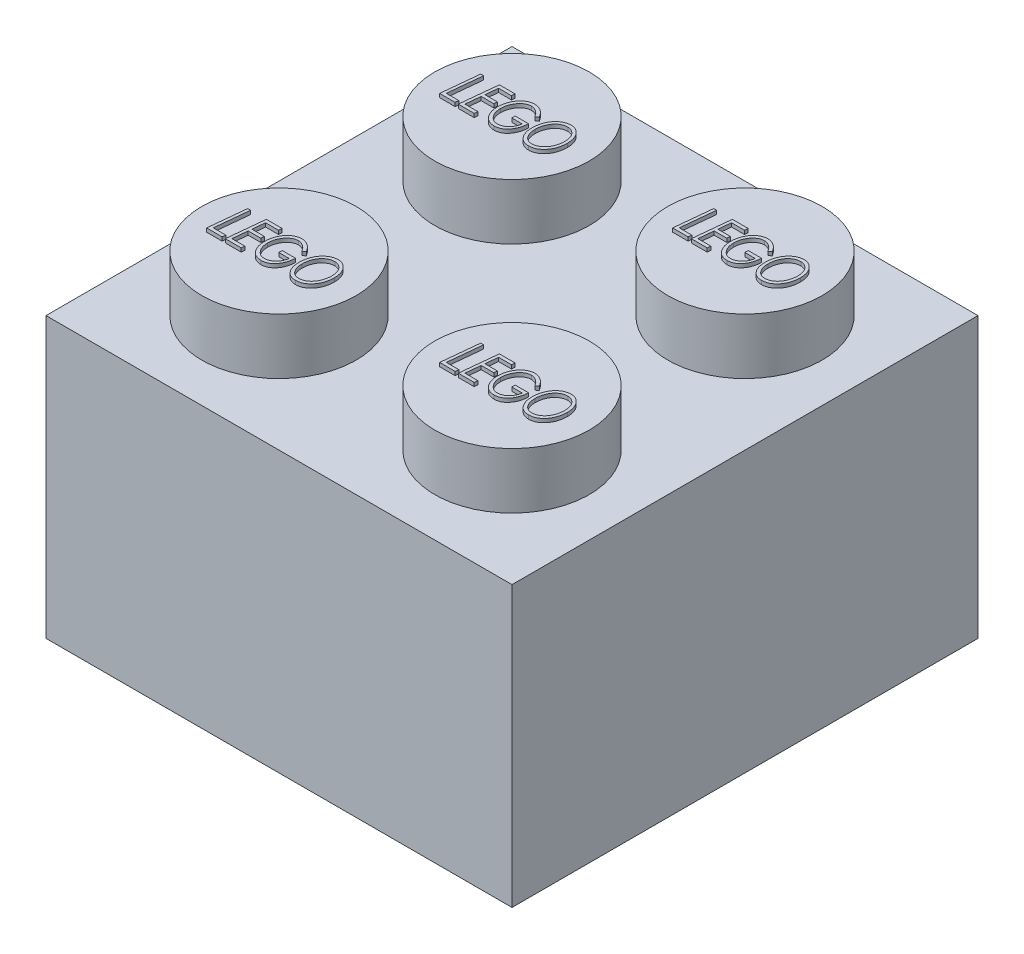
SolidWorks part; units mm, degrees
ref_plane "Front Plane" through (0, 0, 0) normal (0, 0, 1) x (1, 0, 0)
ref_plane "Top Plane" through (0, 0, 0) normal (0, 1, 0) x (1, 0, 0)
ref_plane "Right Plane" through (0, 0, 0) normal (1, 0, 0) x (0, 0, -1)
sketch "Sketch2" plane through (0, 0, 0) normal (0, 1, 0) x (1, 0, 0)
  line L0 (-17.7331, 8.7234) -> (-1.8581, 8.7234)
  line L1 (-1.8581, 8.7234) -> (-1.8581, -7.1516)
  line L2 (-1.8581, -7.1516) -> (-17.7331, -7.1516)
  line L3 (-17.7331, -7.1516) -> (-17.7331, 8.7234)
  dimension "D1" = 15.875
  dimension "D2" = 15.875
extrude "Boss-Extrude3" add sketch "Sketch2" along normal blind 9.525
sketch "Sketch3" plane through (0, 9.525, 0) normal (0, 1, 0) x (1, 0, 0)
  line L0 (-17.7331, 8.7234) -> (-17.7331, -7.1516) construction
  line L1 (-1.8581, 8.7234) -> (-17.7331, 8.7234) construction
  circle A0 centre (-13.7644, 4.7546) radius 2.6308
  dimension "D1" = 3.9687
  dimension "D2" = 3.9688
extrude "Boss-Extrude4" add sketch "Sketch3" along normal blind 1.905
pattern_linear "LPattern1" count 2 spacing 7.9375 along (1, 0, 0) count 2 spacing 7.9375 along (0, 0, 1) of "Boss-Extrude4"
shell "Shell1" thickness 1.524
sketch "Sketch4" plane through (0, 11.43, 0) normal (0, 1, 0) x (1, 0, 0)
  line L1 (-13.7644, 4.7546) -> (-13.7644, 4.0766) construction
  line L2 (-15.584, 4.0766) -> (-11.9447, 4.0766) construction
  text T0 "<i>LEGO</i>" font "Century Gothic" height 1.27
  point P4 (-13.7644, 4.7546)
  point P9 (-13.7644, 4.0766)
extrude "Boss-Extrude5" add sketch "Sketch4" along normal blind 0.127
pattern_linear "LPattern2" count 2 spacing 7.9375 along (1, 0, 0) count 2 spacing 7.9375 along (0, 0, 1) of "Boss-Extrude5"
sketch "Sketch5" plane through (0, 0, 0) normal (0, -1, 0) x (1, 0, 0)
  circle A2 centre (-9.7956, -0.7859) radius 3.175
  circle A3 centre (-9.7956, -0.7859) radius 2.3876
  dimension "D1" = 6.35
  dimension "D2" = 4.7752
extrude "Boss-Extrude6" add sketch "Sketch5" against normal up to surface (8.001 mm away) up to face at (-5.8269, 8.001, -5.8614)
